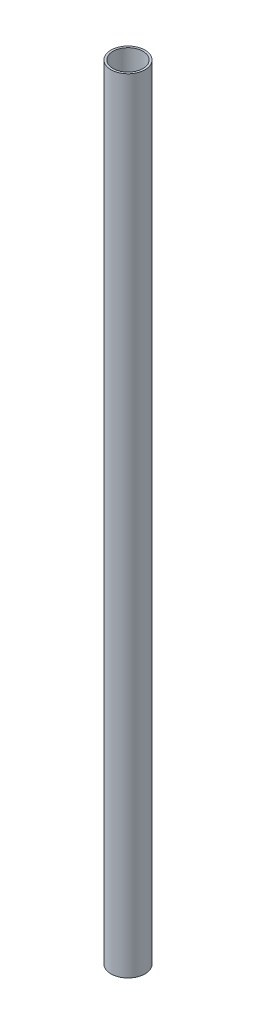
SolidWorks part; units mm, degrees
ref_plane "Front Plane" through (0, 0, 0) normal (0, 0, 1) x (1, 0, 0)
ref_plane "Top Plane" through (0, 0, 0) normal (0, 1, 0) x (1, 0, 0)
ref_plane "Right Plane" through (0, 0, 0) normal (1, 0, 0) x (0, 0, -1)
sketch "Sketch1" plane through (0, 0, 0) normal (0, 1, 0) x (1, 0, 0)
  circle A0 centre (0, 0) radius 12.7
  circle A1 centre (0, 0) radius 11.176
  dimension "D1" = 25.4
  dimension "D2" = 22.352
extrude "Boss-Extrude1" add sketch "Sketch1" along normal blind 584.2
